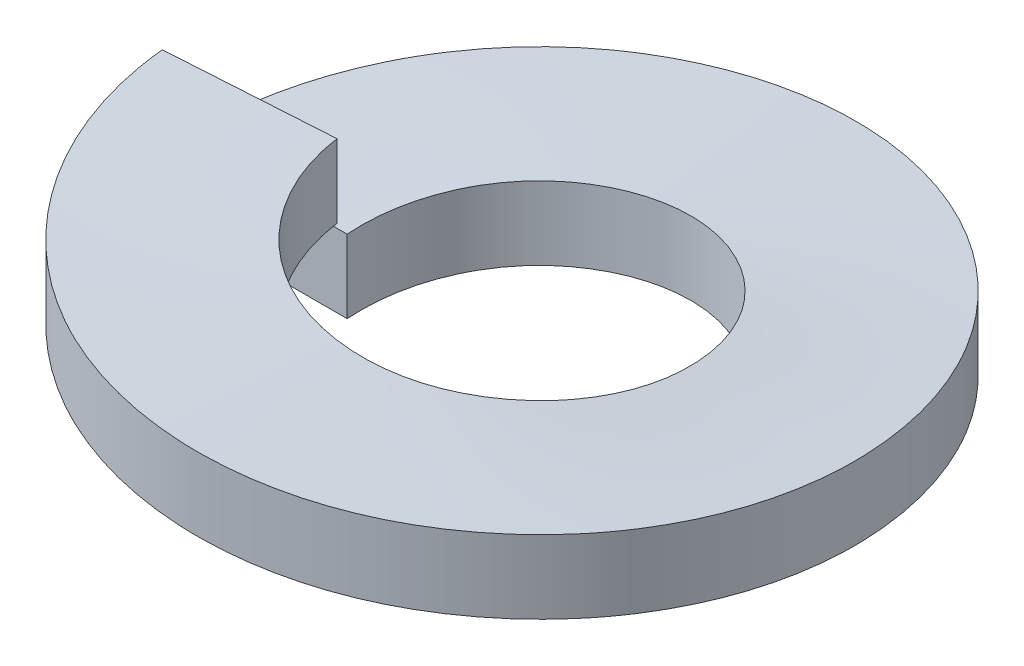
SolidWorks part; units mm, degrees
ref_plane "Front Plane" through (0, 0, 0) normal (0, 0, 1) x (1, 0, 0)
ref_plane "Top Plane" through (0, 0, 0) normal (0, 1, 0) x (1, 0, 0)
ref_plane "Right Plane" through (0, 0, 0) normal (1, 0, 0) x (0, 0, -1)
sketch "Sketch1" plane through (0, 0, 0) normal (0, 0, 1) x (1, 0, 0)
  line L0 (0, 0) -> (0, 0.508) construction
  line L1 (-2.286, 0.508) -> (-1.143, 0.508)
  line L2 (-2.286, 0.508) -> (-2.286, 0)
  line L3 (-2.286, 0) -> (-1.143, 0)
  line L4 (-1.143, 0.508) -> (-1.143, 0)
  dimension "ID" = 2.286
  dimension "OD" = 4.572
  dimension "Min Thickness" = 0.508
sketch "Sketch2" plane through (0, 0, 0) normal (0, 1, 0) x (1, 0, 0)
  circle A0 centre (0, 0) radius 2.286
curve "Helix/Spiral1" pitch 0.6158 height 0.6096 turns 0.99
sweep "Sweep1" add profiles "Sketch1" path "Helix/Spiral1"
ref_plane "Plane1" through (0, 0.254, 0) normal (0, 1, 0) x (-1, 0, 0)
sketch "Sketch3" plane through (0, 0.254, 0) normal (0, 1, 0) x (1, 0, 0)
  circle A0 centre (0, 0) radius 1.143
  circle A1 centre (0, 0) radius 2.286
  point P4 (0, 1.143)
equation "\"D3@Helix/Spiral1\" = \"Min Thickness@Sketch1\"*1.2"
equation "\"D1@Plane1\" = \"Min Thickness@Sketch1\"/2"
